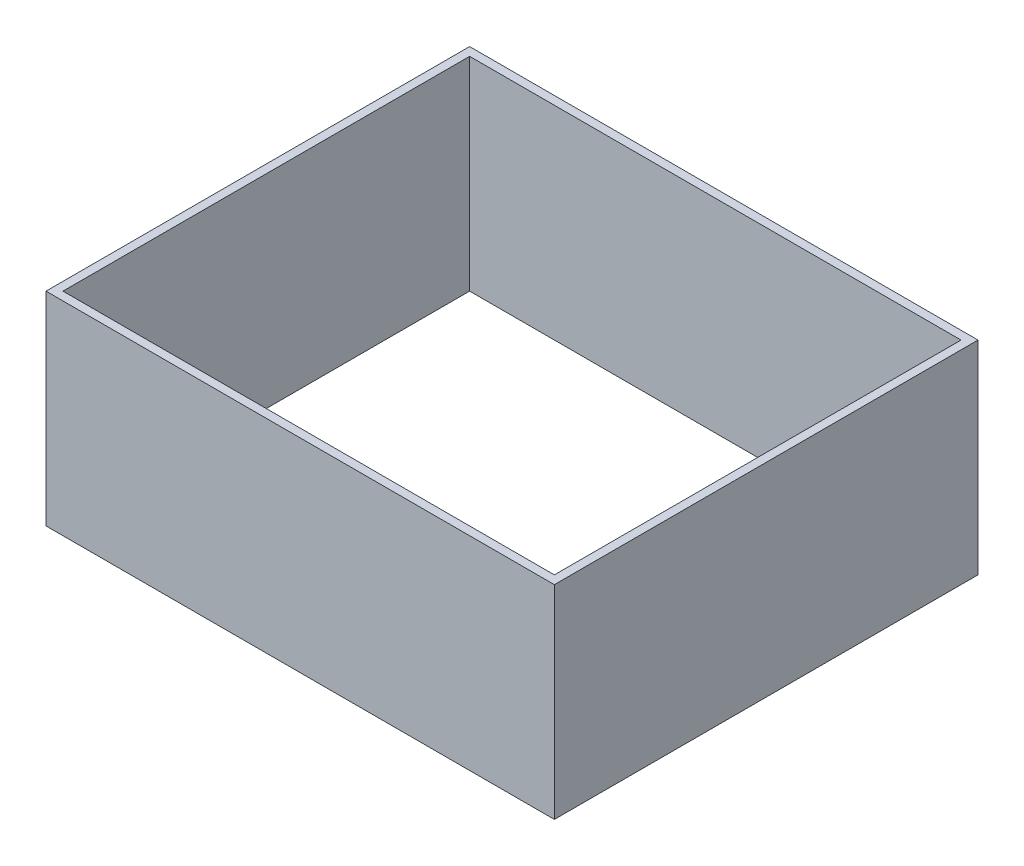
SolidWorks part; units mm, degrees
ref_plane "Front Plane" through (0, 0, 0) normal (0, 0, 1) x (1, 0, 0)
ref_plane "Top Plane" through (0, 0, 0) normal (0, 1, 0) x (1, 0, 0)
ref_plane "Right Plane" through (0, 0, 0) normal (1, 0, 0) x (0, 0, -1)
sketch "Sketch1" plane through (0, 0, 0) normal (0, 1, 0) x (1, 0, 0)
  line L0 (-75, -62.5) -> (-75, 62.5)
  line L1 (0, 0) -> (75, 0) construction
  line L2 (0, -62.5) -> (0, 62.5) construction
  line L3 (-75, 62.5) -> (75, 62.5)
  line L4 (75, -62.5) -> (75, 62.5)
  line L5 (-75, -62.5) -> (-75, 62.5)
  line L6 (75, -62.5) -> (75, 62.5)
  line L7 (-75, -62.5) -> (75, -62.5)
  line L8 (0, 0) -> (-75, 0) construction
  point P10 (-75, 0)
  dimension "D1" = 150
  dimension "D2" = 125
extrude "Boss-Extrude1" add sketch "Sketch1" along normal blind 60 contours L0 L7 L4 L3
shell "Shell1" thickness 2.5
